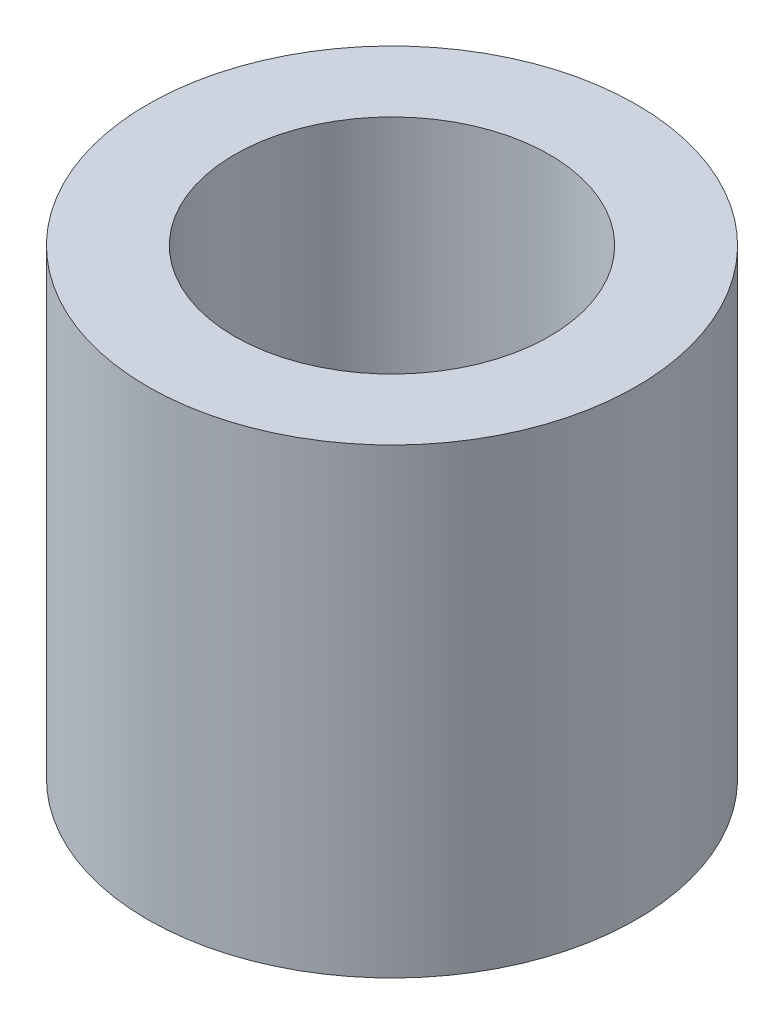
SolidWorks part; units mm, degrees
material "Plain Carbon Steel"
ref_plane "Front Plane" through (0, 0, 0) normal (0, 0, 1) x (1, 0, 0)
ref_plane "Top Plane" through (0, 0, 0) normal (0, 1, 0) x (1, 0, 0)
ref_plane "Right Plane" through (0, 0, 0) normal (1, 0, 0) x (0, 0, -1)
sketch "Sketch1" plane through (0, 0, 0) normal (0, 1, 0) x (1, 0, 0)
  circle A1 centre (0, 0) radius 2.25
  dimension "D2" = 4.5
extrude "Boss-Extrude1" add sketch "Sketch1" along normal blind 4.25
hole_wizard "M2.5 Clearance Hole1" positions "Sketch2" profile "Sketch3" hole size "M2.5" standard "ANSI Metric" end condition through all
sketch "Sketch2" plane through (0, 4.25, 0) normal (0, 1, 0) x (1, 0, 0)
  point P0 (0, 0)
sketch "Sketch3" plane through (0, 4.25, 0) normal (1, 0, 0) x (0, 0, 1)
  line L0 (0, 0) -> (0, 4.25)
  line L1 (0, 4.25) -> (1.45, 4.25)
  line L2 (1.45, 4.25) -> (1.45, 0)
  line L5 (1.45, 0) -> (0, 0)
  line L11 (0, -6.35) -> (0, 107.95) construction
  dimension "Thru Hole Dia." = 2.9
  dimension "Thru Hole Depth" = 4.25
